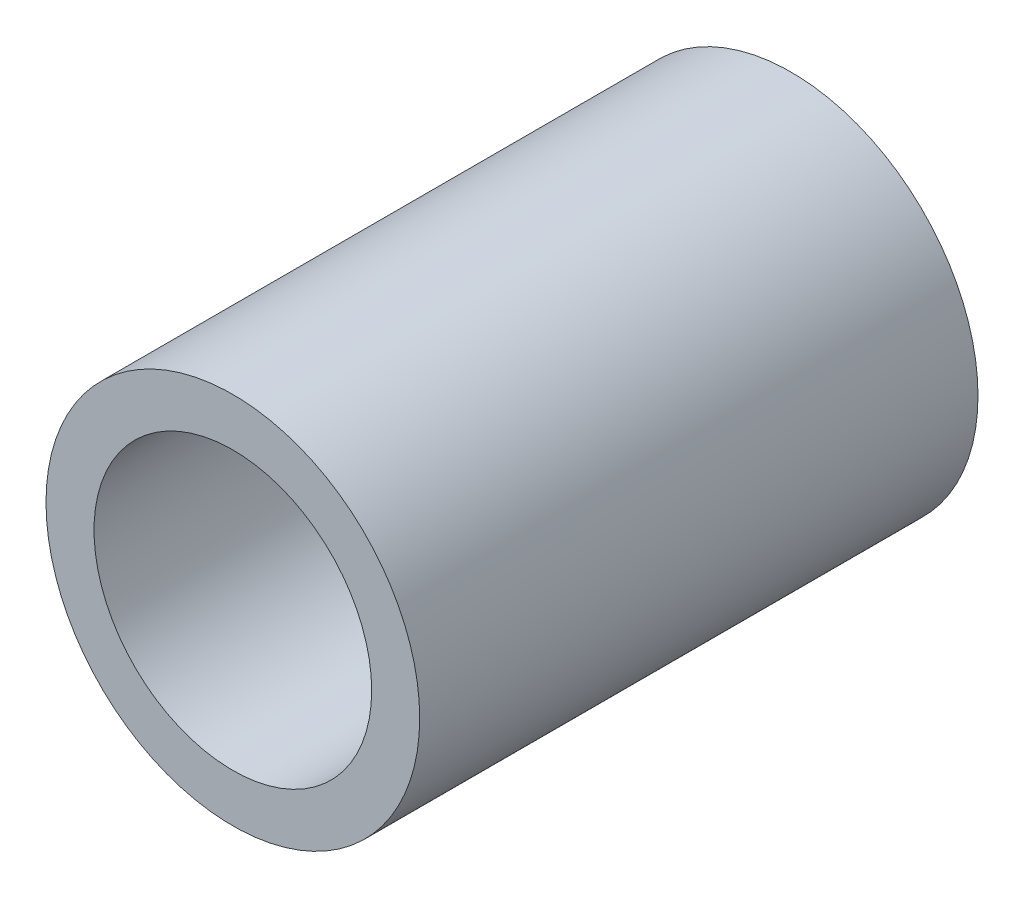
SolidWorks part; units mm, degrees
ref_plane "Front Plane" through (0, 0, 0) normal (0, 0, 1) x (1, 0, 0)
ref_plane "Top Plane" through (0, 0, 0) normal (0, 1, 0) x (1, 0, 0)
ref_plane "Right Plane" through (0, 0, 0) normal (1, 0, 0) x (0, 0, -1)
sketch "Sketch1" plane through (0, 0, 0) normal (0, 0, 1) x (1, 0, 0)
  circle A0 centre (0, 0) radius 3.1877
  circle A1 centre (0, 0) radius 2.3685
  dimension "D1" = 6.3754
  dimension "ID" = 4.7371
extrude "Extrude1" add sketch "Sketch1" along normal mid plane 9.525
sketch "Sketch2" plane through (0, 0, 0) normal (1, 0, 0) x (0, 0, -1)
  line L0 (-4.7625, -2.3685) -> (4.7625, -2.3685) construction
  line L3 (4.7625, 2.3685) -> (-4.7625, 2.3685) construction
  line L5 (-4.7625, -2.3685) -> (4.7625, -2.3685)
  line L6 (4.7625, 2.3685) -> (-4.7625, 2.3685)
sketch "Sketch4" plane through (0, 0, 4.7625) normal (0, 0, 1) x (1, 0, 0)
  line L0 (0, 0) -> (-1.6748, 1.6748)
  line L1 (0, -4.3726) -> (0, 4.3726) construction
  circle A0 centre (0, 0) radius 2.3685 construction
  dimension "D1" = 45
